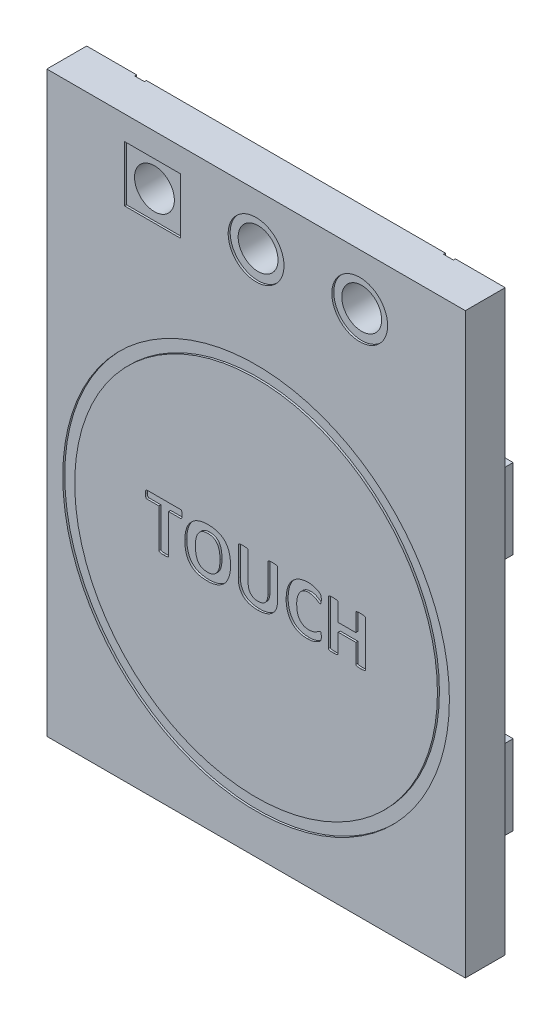
SolidWorks part; units mm, degrees
ref_plane "Спереди" through (0, 0, 0) normal (0, 0, 1) x (1, 0, 0)
ref_plane "Сверху" through (0, 0, 0) normal (0, 1, 0) x (1, 0, 0)
ref_plane "Справа" through (0, 0, 0) normal (1, 0, 0) x (0, 0, -1)
sketch "Эскиз1" plane through (0, 0, 0) normal (0, 0, 1) x (1, 0, 0)
  line L0 (0, 0) -> (0, 7.25) construction
  line L1 (5.25, -7.25) -> (-5.25, -7.25)
  line L2 (5.25, -7.25) -> (5.25, 7.25)
  line L3 (5.25, 7.25) -> (-5.25, 7.25)
  line L4 (-5.25, -7.25) -> (-5.25, 7.25)
  line L5 (5.25, -7.25) -> (-5.25, 7.25) construction
  line L6 (5.25, 7.25) -> (-5.25, -7.25) construction
  line L7 (0, 5.95) -> (2.6, 5.95) construction
  circle A0 centre (0, 5.95) radius 0.5
  circle A1 centre (2.6, 5.95) radius 0.5
  circle A2 centre (-2.6, 5.95) radius 0.5
  point P0 (0, 0)
  dimension "D3" = 1
  dimension "D4" = 5.2
  dimension "D1" = 10.5
  dimension "D2" = 14.5
  dimension "D5" = 1.3
extrude "Бобышка-Вытянуть1" add sketch "Эскиз1" along normal blind 1
sketch "Эскиз2" plane through (0, 0, 1) normal (0, 0, 1) x (1, 0, 0)
  line L0 (0, -7.25) -> (0, 3.0919) construction
  line L1 (-5.25, -7.25) -> (5.25, -7.25) construction
  circle A0 centre (0, -1.4) radius 4.85
  circle A1 centre (0, -1.4) radius 4.55
  dimension "D1" = 9.7
  dimension "D2" = 1
  dimension "D3" = 0.3
extrude "Вырез-Вытянуть1" cut sketch "Эскиз2" against normal blind 0.05
sketch "Эскиз3" plane through (0, 0, 0) normal (0, 0, -1) x (-1, 0, 0)
  line L0 (5.25, 7.25) -> (5.25, -7.25) construction
  line L1 (2.95, 3.05) -> (4.25, 3.05)
  line L2 (2.95, 3.05) -> (2.95, 1.05)
  line L3 (2.95, 1.05) -> (4.25, 1.05)
  line L4 (4.25, 3.05) -> (4.25, 1.05)
  line L5 (-1.5, -3.75) -> (1.5, -3.75)
  line L6 (-1.5, -3.75) -> (-1.5, -5.75)
  line L7 (-1.5, -5.75) -> (1.5, -5.75)
  line L8 (1.5, -3.75) -> (1.5, -5.75)
  line L9 (-4.45, -3.45) -> (-3.15, -3.45)
  line L10 (-4.45, -3.45) -> (-4.45, -5.45)
  line L11 (-4.45, -5.45) -> (-3.15, -5.45)
  line L12 (-3.15, -3.45) -> (-3.15, -5.45)
  line L13 (-4.45, 2.55) -> (-3.15, 2.55)
  line L14 (-4.45, 2.55) -> (-4.45, 0.55)
  line L15 (-4.45, 0.55) -> (-3.15, 0.55)
  line L16 (-3.15, 2.55) -> (-3.15, 0.55)
  line L17 (-5.25, 7.25) -> (5.25, 7.25) construction
  line L18 (-5.25, -7.25) -> (-5.25, 7.25) construction
  line L19 (5.25, -7.25) -> (-5.25, -7.25) construction
  line L20 (0, -5.75) -> (0, -7.25) construction
  dimension "D1" = 1.3
  dimension "D2" = 1
  dimension "D3" = 2
  dimension "D4" = 4.2
  dimension "D5" = 0.8
  dimension "D6" = 4.7
  dimension "D7" = 1.8
  dimension "D8" = 2
  dimension "D9" = 3
  dimension "D10" = 1.5
extrude "Бобышка-Вытянуть2" add sketch "Эскиз3" along normal blind 1
sketch "Эскиз4" plane through (0, 0, 0) normal (0, 0, -1) x (-1, 0, 0)
  line L1 (3.3, 6.65) -> (1.9, 6.65)
  line L2 (3.3, 6.65) -> (3.3, 5.25)
  line L3 (3.3, 5.25) -> (1.9, 5.25)
  line L4 (1.9, 6.65) -> (1.9, 5.25)
  line L5 (3.3, 6.65) -> (1.9, 5.25) construction
  line L6 (3.3, 5.25) -> (1.9, 6.65) construction
  circle A0 centre (0, 5.95) radius 0.7
  circle A1 centre (-2.6, 5.95) radius 0.7
  circle A2 centre (0, 5.95) radius 0.5 construction
  point P0 (2.6, 5.95)
  dimension "D1" = 0.2
extrude "Вырез-Вытянуть2" cut sketch "Эскиз4" against normal blind 0.05
sketch "Эскиз5" plane through (0, 0, 0) normal (0, 0, -1) x (-1, 0, 0)
  line L0 (268.6596, -118.9819) -> (268.6596, -624.3152) construction
  line L1 (0, 7.25) -> (0, -7.25) construction
  line L2 (-5.25, 7.25) -> (5.25, 7.25) construction
  line L3 (5.25, -7.25) -> (-5.25, -7.25) construction
  line L4 (4, 7.25) -> (4, 4.4)
  line L5 (4, 4.4) -> (-4, 4.4)
  line L6 (4, 7.25) -> (3.75, 7.25)
  line L7 (3.75, 7.25) -> (3.75, 4.65)
  line L8 (3.75, 4.65) -> (-3.75, 4.65)
  line L9 (-3.75, 7.25) -> (-3.75, 4.65)
  line L10 (-4, 7.25) -> (-3.75, 7.25)
  line L11 (-4, 7.25) -> (-4, 4.4)
  line L12 (1.8112, 4.65) -> (1.8112, 4.4) construction
  line L13 (1.5, 4.1506) -> (1.5, -0.9208) construction
  line L14 (-0.5, 4.1506) -> (-0.5, 0.9953) construction
  line L15 (-2.5, 4.1506) -> (-2.5, 0.4969) construction
  text T0 "GND" font "Calibri" height 1
  text T1 "I/O" font "Calibri" height 1
  text T2 "VCO" font "Calibri" height 1
  point P15 (0, 4.65)
  point P18 (0, 4.4)
  dimension "D1" = 0.25
  dimension "D2" = 2.85
  dimension "D3" = 8
  dimension "D4" = 1.5
  dimension "D5" = 2
  dimension "D6" = 2
extrude "Вырез-Вытянуть3" cut sketch "Эскиз5" against normal blind 0.05
sketch "Эскиз6" plane through (0, 0, 1) normal (0, 0, 1) x (1, 0, 0)
  line L0 (108.0123, 253.5387) -> (641.3456, 253.5387) construction
  line L1 (-1.9, 5.25) -> (-3.3, 5.25) construction
  line L2 (-1.9, 6.65) -> (-1.9, 5.25) construction
  line L3 (-3.3, 6.65) -> (-1.9, 6.65) construction
  line L4 (-3.3, 5.25) -> (-3.3, 6.65) construction
  line L5 (-1.9, 5.25) -> (-3.3, 5.25)
  line L6 (-1.9, 6.65) -> (-1.9, 5.25)
  line L7 (-3.3, 6.65) -> (-1.9, 6.65)
  line L8 (-3.3, 5.25) -> (-3.3, 6.65)
  line L9 (-2.7931, -1.8431) -> (7.6685, -1.8431) construction
  circle A0 centre (2.6, 5.95) radius 0.7 construction
  circle A1 centre (0, 5.95) radius 0.7 construction
  circle A2 centre (2.6, 5.95) radius 0.7
  circle A3 centre (0, 5.95) radius 0.7
  text T0 "TOUCH" font "Calibri" height 1.2
extrude "Вырез-Вытянуть4" cut sketch "Эскиз6" against normal blind 0.05
